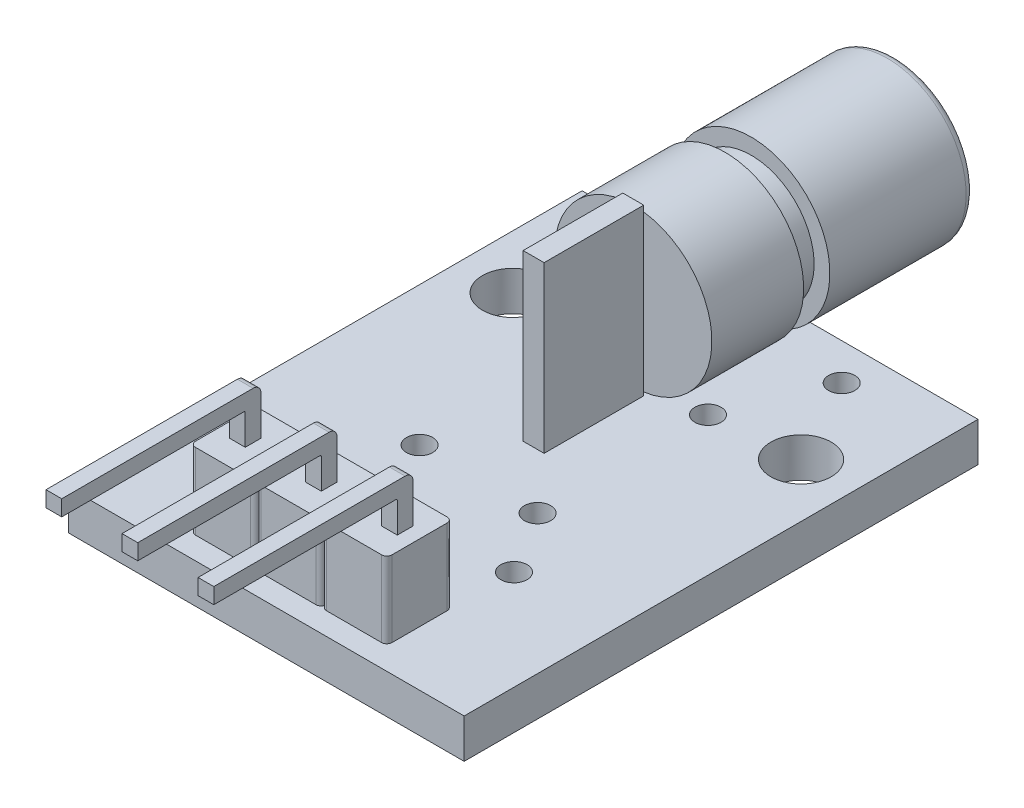
SolidWorks part; units mm, degrees
ref_plane "Front Plane" through (0, 0, 0) normal (0, 0, 1) x (1, 0, 0)
ref_plane "Top Plane" through (0, 0, 0) normal (0, 1, 0) x (1, 0, 0)
ref_plane "Right Plane" through (0, 0, 0) normal (1, 0, 0) x (0, 0, -1)
sketch "Sketch1" plane through (0, 0, 0) normal (0, 1, 0) x (1, 0, 0)
  line L1 (-7.55, -9.8) -> (7.55, -9.8)
  line L2 (-7.55, -9.8) -> (-7.55, 9.8)
  line L3 (-7.55, 9.8) -> (7.55, 9.8)
  line L4 (7.55, -9.8) -> (7.55, 9.8)
  line L5 (-7.55, -9.8) -> (7.55, 9.8) construction
  line L6 (-7.55, 9.8) -> (7.55, -9.8) construction
  point P0 (0, 0)
  dimension "D1" = 15.1
  dimension "D2" = 19.6
extrude "Boss-Extrude1" add sketch "Sketch1" along normal blind 1.5
sketch "Sketch2" plane through (0, 0, 0) normal (0, -1, 0) x (1, 0, 0)
  line L0 (0.3, 7.4) -> (3.2, 7.4) construction
  line L1 (-0.3, 8) -> (0.3, 8)
  line L2 (-0.3, 8) -> (-0.3, 7.4)
  line L3 (-0.3, 7.4) -> (0.3, 7.4)
  line L4 (0.3, 8) -> (0.3, 7.4)
  line L5 (-0.3, 8) -> (0.3, 7.4) construction
  line L6 (-0.3, 7.4) -> (0.3, 8) construction
  line L7 (3.2, 8) -> (2.6, 8)
  line L8 (3.2, 8) -> (3.2, 7.4)
  line L9 (3.2, 7.4) -> (2.6, 7.4)
  line L10 (2.6, 8) -> (2.6, 7.4)
  line L11 (3.2, 8) -> (2.6, 7.4) construction
  line L12 (3.2, 7.4) -> (2.6, 8) construction
  line L13 (-3.2, 8) -> (-2.6, 8)
  line L14 (-3.2, 8) -> (-3.2, 7.4)
  line L15 (-3.2, 7.4) -> (-2.6, 7.4)
  line L16 (-2.6, 8) -> (-2.6, 7.4)
  line L17 (-3.2, 8) -> (-2.6, 7.4) construction
  line L18 (-3.2, 7.4) -> (-2.6, 8) construction
  line L19 (-2.6, 7.4) -> (-0.3, 7.4) construction
  line L20 (0, 0) -> (0, 7.4) construction
  line L21 (-7.55, 9.8) -> (7.55, 9.8) construction
  line L22 (0.3, 8) -> (2.6, 8) construction
  line L23 (-2.6, 8) -> (-0.3, 8) construction
  point P0 (0, 7.7)
  point P5 (2.9, 7.7)
  point P10 (-2.9, 7.7)
  dimension "D1" = 0.6
  dimension "D2" = 0.6
  dimension "D3" = 2.4
  dimension "D4" = 5.8
extrude "Boss-Extrude2" add sketch "Sketch2" along normal blind 1.7
sketch "Sketch3" plane through (0, 1.5, 0) normal (0, 1, 0) x (1, 0, 0)
  line L0 (0.3, -8) -> (-0.3, -7.4) construction
  line L2 (-3.75, -8.95) -> (-3.75, -6.45)
  line L4 (3.75, -8.95) -> (3.75, -6.45)
  line L5 (-3.75, -8.95) -> (3.75, -6.45) construction
  line L6 (-3.75, -6.45) -> (3.75, -8.95) construction
  line L7 (-3.75, -6.45) -> (-1.45, -6.45)
  line L8 (-1.05, -6.45) -> (1.05, -6.45)
  line L9 (1.45, -6.45) -> (3.75, -6.45)
  line L10 (-1.05, -6.45) -> (-1.45, -6.45) construction
  line L11 (1.45, -6.45) -> (1.05, -6.45) construction
  line L12 (-3.75, -8.95) -> (-1.45, -8.95)
  line L13 (-1.05, -8.95) -> (1.05, -8.95)
  line L14 (1.45, -8.95) -> (3.75, -8.95)
  line L15 (-1.05, -8.95) -> (-1.45, -8.95) construction
  line L16 (1.45, -8.95) -> (1.05, -8.95) construction
  line L17 (-1.25, -8.75) -> (-1.25, -6.65) construction
  line L18 (1.25, -8.75) -> (1.25, -6.65) construction
  line L19 (1.25, -8.75) -> (-1.25, -8.75) construction
  line L20 (1.25, -6.65) -> (-1.25, -6.65) construction
  line L21 (0, -7.7) -> (0, -8.95) construction
  arc A0 (-1.45, -6.45) -> (-1.25, -6.65) centre (-1.45, -6.65) cw
  arc A1 (-1.25, -6.65) -> (-1.05, -6.45) centre (-1.05, -6.65) cw
  arc A2 (1.05, -6.45) -> (1.25, -6.65) centre (1.05, -6.65) cw
  arc A3 (1.25, -6.65) -> (1.45, -6.45) centre (1.45, -6.65) cw
  arc A4 (-1.45, -8.95) -> (-1.25, -8.75) centre (-1.45, -8.75) ccw
  arc A5 (-1.25, -8.75) -> (-1.05, -8.95) centre (-1.05, -8.75) ccw
  arc A6 (1.05, -8.95) -> (1.25, -8.75) centre (1.05, -8.75) ccw
  arc A7 (1.25, -8.75) -> (1.45, -8.95) centre (1.45, -8.75) ccw
  point P0 (0, -7.7)
  point P33 (1.0502, -6.45)
  dimension "D3" = 0.2
  dimension "D4" = 0.2
  dimension "D1" = 7.5
  dimension "D2" = 2.5
extrude "Boss-Extrude3" add sketch "Sketch3" along normal blind 2.9
sketch "Sketch4" plane through (0, 4.4, 0) normal (0, 1, 0) x (1, 0, 0)
  line L1 (-3.2, -8) -> (-2.6, -8)
  line L2 (-3.2, -8) -> (-3.2, -7.4)
  line L3 (-3.2, -7.4) -> (-2.6, -7.4)
  line L4 (-2.6, -8) -> (-2.6, -7.4)
  line L5 (-0.3, -8) -> (0.3, -8)
  line L6 (-0.3, -8) -> (-0.3, -7.4)
  line L7 (-0.3, -7.4) -> (0.3, -7.4)
  line L8 (0.3, -8) -> (0.3, -7.4)
  line L9 (2.6, -8) -> (3.2, -8)
  line L10 (2.6, -8) -> (2.6, -7.4)
  line L11 (2.6, -7.4) -> (3.2, -7.4)
  line L12 (3.2, -8) -> (3.2, -7.4)
extrude "Boss-Extrude4" add sketch "Sketch4" along normal blind 1.8
sketch "Sketch5" plane through (0, 0, 8) normal (0, 0, 1) x (1, 0, 0)
  line L0 (-2.6, 6.2) -> (-2.6, 4.4) construction
  line L1 (-3.2, 6.2) -> (-2.6, 6.2)
  line L2 (-3.2, 6.2) -> (-3.2, 5.6)
  line L3 (-3.2, 5.6) -> (-2.6, 5.6)
  line L4 (-2.6, 6.2) -> (-2.6, 5.6)
  line L5 (0.3, 6.2) -> (0.3, 4.4) construction
  line L6 (-0.3, 6.2) -> (0.3, 6.2)
  line L7 (-0.3, 6.2) -> (-0.3, 5.6)
  line L8 (-0.3, 5.6) -> (0.3, 5.6)
  line L9 (0.3, 6.2) -> (0.3, 5.6)
  line L10 (3.2, 6.2) -> (3.2, 4.4) construction
  line L11 (2.6, 6.2) -> (3.2, 6.2)
  line L12 (2.6, 6.2) -> (2.6, 5.6)
  line L13 (2.6, 5.6) -> (3.2, 5.6)
  line L14 (3.2, 6.2) -> (3.2, 5.6)
  line L15 (-2.6, 5.6) -> (-0.3, 5.6) construction
  line L16 (0.3, 5.6) -> (2.6, 5.6) construction
extrude "Boss-Extrude5" add sketch "Sketch5" along normal blind 7
sketch "Sketch7" plane through (0, 1.5, 0) normal (0, 1, 0) x (1, 0, 0)
  line L0 (7.55, 9.8) -> (-7.55, 9.8) construction
  line L1 (0.4, 4.2) -> (-0.4, 4.2)
  line L2 (0.4, 4.2) -> (0.4, 0.4)
  line L3 (0.4, 0.4) -> (-0.4, 0.4)
  line L4 (-0.4, 4.2) -> (-0.4, 0.4)
  line L5 (0.4, 4.2) -> (-0.4, 0.4) construction
  line L6 (0.4, 0.4) -> (-0.4, 4.2) construction
  line L7 (0, 0) -> (0, 0.4) construction
  point P0 (0, 2.3)
  dimension "D1" = 9.4
  dimension "D2" = 3.8
  dimension "D3" = 0.8
extrude "Boss-Extrude6" add sketch "Sketch7" along normal blind 6.3
sketch "Sketch8" plane through (0, 0, -4.2) normal (0, 0, -1) x (-1, 0, 0)
  line L0 (0, 4.6) -> (0, 0) construction
  circle A0 centre (0, 4.6) radius 3
  dimension "D1" = 6
  dimension "D2" = 4.6
extrude "Boss-Extrude7" add sketch "Sketch8" along normal blind 3.5
sketch "Sketch9" plane through (0, 0, -7.7) normal (0, 0, -1) x (-1, 0, 0)
  circle A0 centre (0, 4.6) radius 2.4
  dimension "D1" = 4.8
extrude "Boss-Extrude8" add sketch "Sketch9" along normal blind 1
sketch "Sketch10" plane through (0, 0, -8.7) normal (0, 0, -1) x (-1, 0, 0)
  circle A0 centre (0, 4.6) radius 3
  circle A1 centre (0, 4.6) radius 3 construction
extrude "Boss-Extrude9" add sketch "Sketch10" along normal blind 5.5
fillet "Fillet1" radius 0.3 1 edges at (-3, 4.6, -14.2)
sketch "Sketch11" plane through (0, 0, -14.2) normal (0, 0, -1) x (-1, 0, 0)
  circle A0 centre (0, 4.6) radius 1.5
  dimension "D1" = 3
extrude "Cut-Extrude1" cut sketch "Sketch11" against normal blind 1
sketch "Sketch12" plane through (0, 1.5, 0) normal (0, 1, 0) x (1, 0, 0)
  line L0 (-5.5, 5.1) -> (5.5, 5.1) construction
  line L1 (7.55, 9.8) -> (-7.55, 9.8) construction
  line L2 (0, 5.1) -> (0, 0) construction
  circle A0 centre (-5.5, 5.1) radius 1.15
  circle A1 centre (5.5, 5.1) radius 1.15
  dimension "D2" = 2.3
  dimension "D1" = 4.7
  dimension "D3" = 11
extrude "Cut-Extrude2" cut sketch "Sketch12" against normal through all
sketch "Sketch13" plane through (0, 0, 0) normal (0, -1, 0) x (1, 0, 0)
  line L0 (2.25, 1.7) -> (-2.25, -4.8) construction
  line L1 (2.25, 1.7) -> (-2.25, 1.7) construction
  line L2 (2.25, 1.7) -> (2.25, -4.8) construction
  line L3 (2.25, -4.8) -> (-2.25, -4.8) construction
  line L4 (-2.25, 1.7) -> (-2.25, -4.8) construction
  line L5 (-2.25, 1.7) -> (2.25, -4.8) construction
  line L6 (7.55, -9.8) -> (-7.55, -9.8) construction
  line L7 (0, 0) -> (0, -4.8) construction
  circle A0 centre (-2.25, -4.8) radius 0.5
  circle A1 centre (2.25, -4.8) radius 0.5
  circle A2 centre (2.25, 1.7) radius 0.5
  circle A3 centre (-2.25, 1.7) radius 0.5
  dimension "D3" = 1
  dimension "D1" = 5
  dimension "D2" = 6.5
  dimension "D4" = 4.5
extrude "Cut-Extrude3" cut sketch "Sketch13" against normal up to next
sketch "Sketch14" plane through (0, 0, 0) normal (0, -1, 0) x (1, 0, 0)
  line L0 (0, 0) -> (0, -2.15) construction
  line L1 (-3.75, -8.4) -> (3.75, -8.4) construction
  line L2 (-3.75, -8.4) -> (-3.75, 4.1) construction
  line L3 (-3.75, 4.1) -> (3.75, 4.1) construction
  line L4 (3.75, -8.4) -> (3.75, 4.1) construction
  line L5 (-3.75, -8.4) -> (3.75, 4.1) construction
  line L6 (-3.75, 4.1) -> (3.75, -8.4) construction
  line L7 (7.55, -9.8) -> (-7.55, -9.8) construction
  circle A0 centre (3.75, 4.1) radius 0.5
  circle A1 centre (-3.75, 4.1) radius 0.5
  circle A2 centre (-3.75, -8.4) radius 0.5
  circle A3 centre (3.75, -8.4) radius 0.5
  point P0 (0, -2.15)
  dimension "D1" = 1
  dimension "D2" = 7.5
  dimension "D3" = 12.5
  dimension "D4" = 1.4
extrude "Cut-Extrude4" cut sketch "Sketch14" against normal up to next
fillet "Fillet2" radius 0.2 4 edges at (3.75, 2.95, 6.45) (3.75, 2.95, 8.95) (-3.75, 2.95, 8.95) (-3.75, 2.95, 6.45)
fillet "Fillet3" radius 0.05 3 edges at (-2.9, 5.6, 8) (0, 5.6, 8) (2.9, 5.6, 8)
fillet "Fillet5" radius 0.3 3 edges at (2.9, 6.2, 7.4) (-2.9, 6.2, 7.4) (0, 6.2, 7.4)
